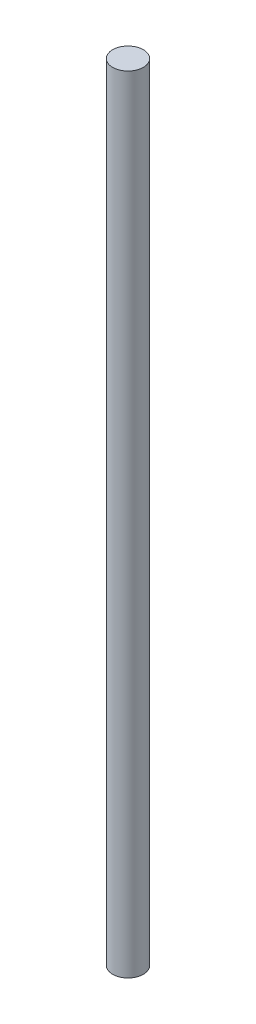
SolidWorks part; units mm, degrees
ref_plane "Front Plane" through (0, 0, 0) normal (0, 0, 1) x (1, 0, 0)
ref_plane "Top Plane" through (0, 0, 0) normal (0, 1, 0) x (1, 0, 0)
ref_plane "Right Plane" through (0, 0, 0) normal (1, 0, 0) x (0, 0, -1)
sketch "Sketch1" plane through (0, 0, 0) normal (0, 1, 0) x (1, 0, 0)
  circle A0 centre (0, 0) radius 3.9688
  dimension "D1" = 7.9375
extrude "Boss-Extrude1" add sketch "Sketch1" along normal blind 203.2
